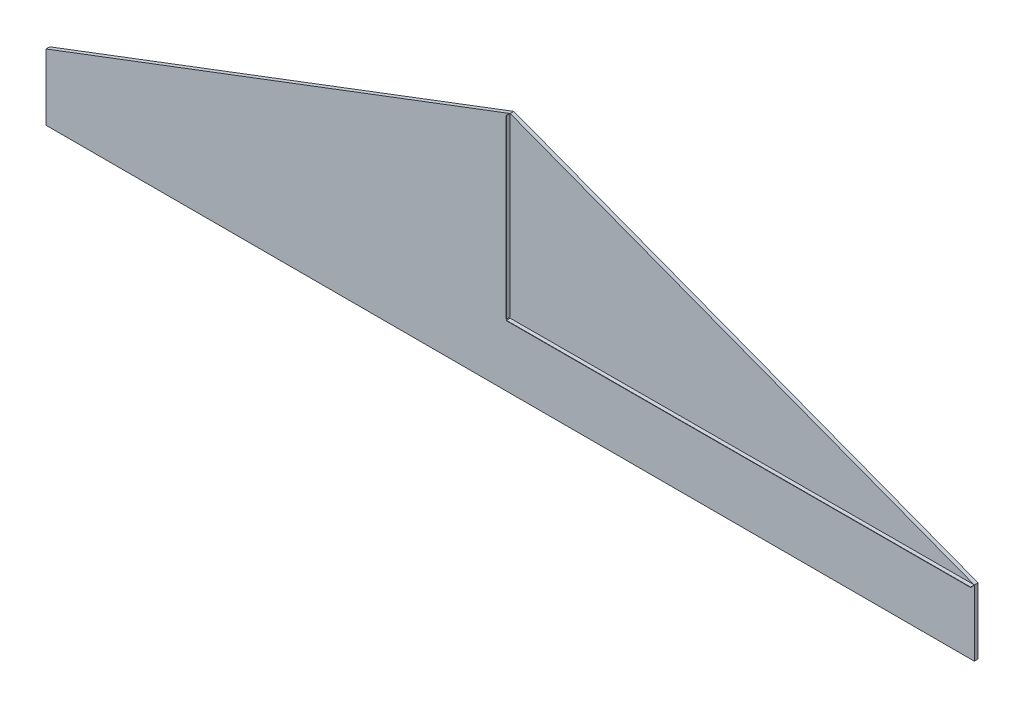
SolidWorks part; units mm, degrees
ref_plane "Alzado" through (0, 0, 0) normal (0, 0, 1) x (1, 0, 0)
ref_plane "Planta" through (0, 0, 0) normal (0, 1, 0) x (1, 0, 0)
ref_plane "Vista lateral" through (0, 0, 0) normal (1, 0, 0) x (0, 0, -1)
sketch "Croquis5" plane through (0, 0, 0) normal (0, 0, 1) x (1, 0, 0)
  line L3 (-12500, 0) -> (12500, 0) construction
  line L4 (12500, 0) -> (0, 4744.1438)
  line L5 (0, 4744.1438) -> (-12500, 0)
  line L6 (-12500, 0) -> (-12500, -1780)
  line L7 (12500, 0) -> (12500, -1780)
  line L8 (-12500, -1780) -> (12500, -1780)
  point P4 (0, 0)
  dimension "D1" = 25000
  dimension "D2" = 13370
  dimension "D3" = 1780
  dimension "D4" = 1780
extrude "Saliente-Extruir1" add sketch "Croquis5" along normal blind 100
sketch "Croquis6" plane through (0, 0, 100) normal (0, 0, 1) x (1, 0, 0)
  line L0 (0, 4744.1438) -> (0, 0)
  line L1 (0, -29.3348) -> (12500, 0)
extrude "Extruir-Lámina1" add sketch "Croquis6" along normal blind 100 thin
